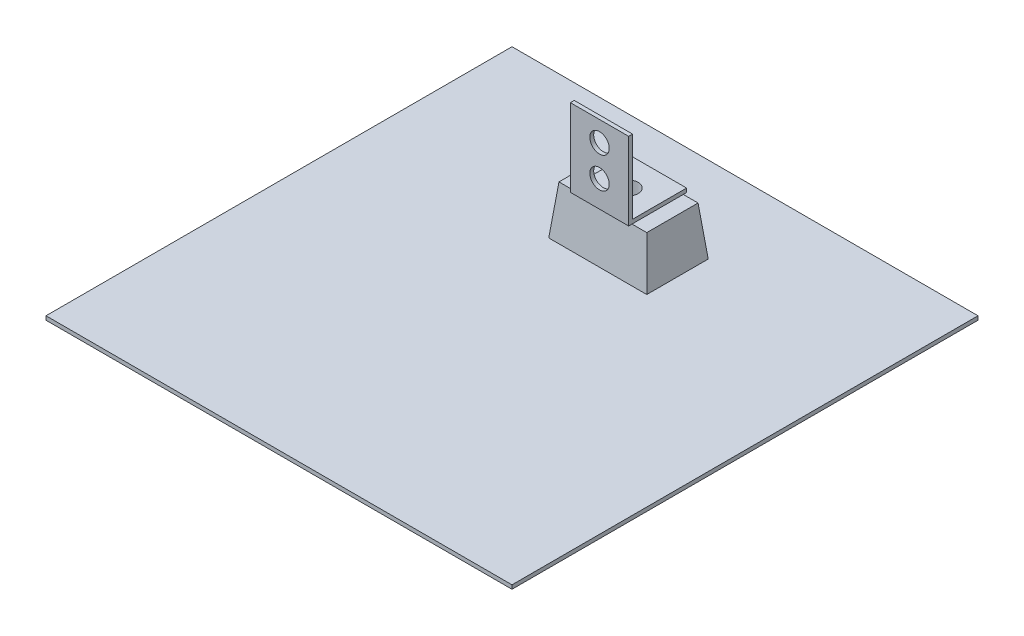
SolidWorks part; units mm, degrees
ref_plane "Front Plane" through (0, 0, 0) normal (0, 0, 1) x (1, 0, 0)
ref_plane "Top Plane" through (0, 0, 0) normal (0, 1, 0) x (1, 0, 0)
ref_plane "Right Plane" through (0, 0, 0) normal (1, 0, 0) x (0, 0, -1)
sketch "Sketch1" plane through (0, 0, 0) normal (0, 1, 0) x (1, 0, 0)
  line L0 (152.4, 304.8) -> (152.4, 228.6) construction
  line L1 (0, 0) -> (304.8, 0)
  line L2 (0, 0) -> (0, 304.8)
  line L3 (0, 304.8) -> (304.8, 304.8)
  line L4 (304.8, 0) -> (304.8, 304.8)
  line L5 (152.4, 228.6) -> (0, 228.6) construction
extrude "Boss-Extrude1" add sketch "Sketch1" along normal blind 2.54
sketch "Sketch2" plane through (0, 2.54, 0) normal (0, 1, 0) x (1, 0, 0)
  line L0 (152.4, 304.8) -> (152.4, 228.6) construction
  line L1 (304.8, 304.8) -> (0, 304.8) construction
  line L3 (120.3451, 208.4935) -> (184.4549, 208.4935)
  line L4 (120.3451, 208.4935) -> (120.3451, 248.7065)
  line L5 (120.3451, 248.7065) -> (184.4549, 248.7065)
  line L6 (184.4549, 208.4935) -> (184.4549, 248.7065)
  line L7 (120.3451, 208.4935) -> (184.4549, 248.7065) construction
  line L8 (120.3451, 248.7065) -> (184.4549, 208.4935) construction
extrude "Boss-Extrude2" add sketch "Sketch2" along normal blind 31.75 draft 6
sketch "Sketch3" plane through (0, 34.29, 0) normal (0, 1, 0) x (1, 0, 0)
  line L0 (152.4, 245.3695) -> (152.4, 211.8305) construction
  line L1 (181.1178, 245.3695) -> (123.6822, 245.3695) construction
  line L2 (123.6822, 211.8305) -> (181.1178, 211.8305) construction
  circle A0 centre (152.4, 228.6) radius 6.35
extrude "Cut-Extrude1" cut sketch "Sketch3" against normal blind 25.4
ref_plane "Plane1" through (152.4, 0, 0) normal (1, 0, 0) x (0, 0, -1)
sketch "Sketch4" plane through (152.4, 0, 0) normal (1, 0, 0) x (0, 0, -1)
  line L0 (209.6487, 34.29) -> (247.5513, 34.29)
  line L1 (209.6487, 34.29) -> (209.6487, 85.09)
  line L3 (212.1887, 36.83) -> (247.5513, 36.83)
  line L4 (212.1887, 36.83) -> (212.1887, 77.47)
  line L6 (247.5513, 36.83) -> (247.5513, 34.29)
  line L7 (209.6487, 34.29) -> (209.6487, 77.47) construction
  line L8 (209.6487, 85.09) -> (212.1887, 85.09)
  line L9 (212.1887, 85.09) -> (212.1887, 77.47)
  point P3 (228.6, 34.29)
  dimension "D1" = 2.54
extrude "Boss-Extrude3" add sketch "Sketch4" along normal blind 19.05 and the other way blind 19.05
sketch "Sketch5" plane through (0, 36.83, 0) normal (0, 1, 0) x (1, 0, 0)
  line L0 (171.45, 228.6) -> (133.35, 228.6) construction
  line L1 (171.45, 211.8305) -> (171.45, 245.3695) construction
  line L2 (133.35, 247.5513) -> (133.35, 212.1887) construction
  circle A0 centre (152.4, 228.6) radius 6.35
extrude "Cut-Extrude2" cut sketch "Sketch5" against normal blind 50.8
sketch "Sketch6" plane through (0, 0, -212.1887) normal (0, 0, -1) x (-1, 0, 0)
  line L0 (-152.4, 83.2947) -> (-152.4, 71.8647) construction
  line L1 (-152.4, 46.7995) -> (-152.4, -46.7995) construction
  line L2 (-152.4, 71.8647) -> (-152.4, 51.5447) construction
  circle A0 centre (-152.4, 71.8647) radius 6.35
  circle A1 centre (-152.4, 51.5447) radius 6.35
  point P7 (0, 0)
  point P8 (0, 0)
extrude "Cut-Extrude3" cut sketch "Sketch6" against normal blind 19.05
